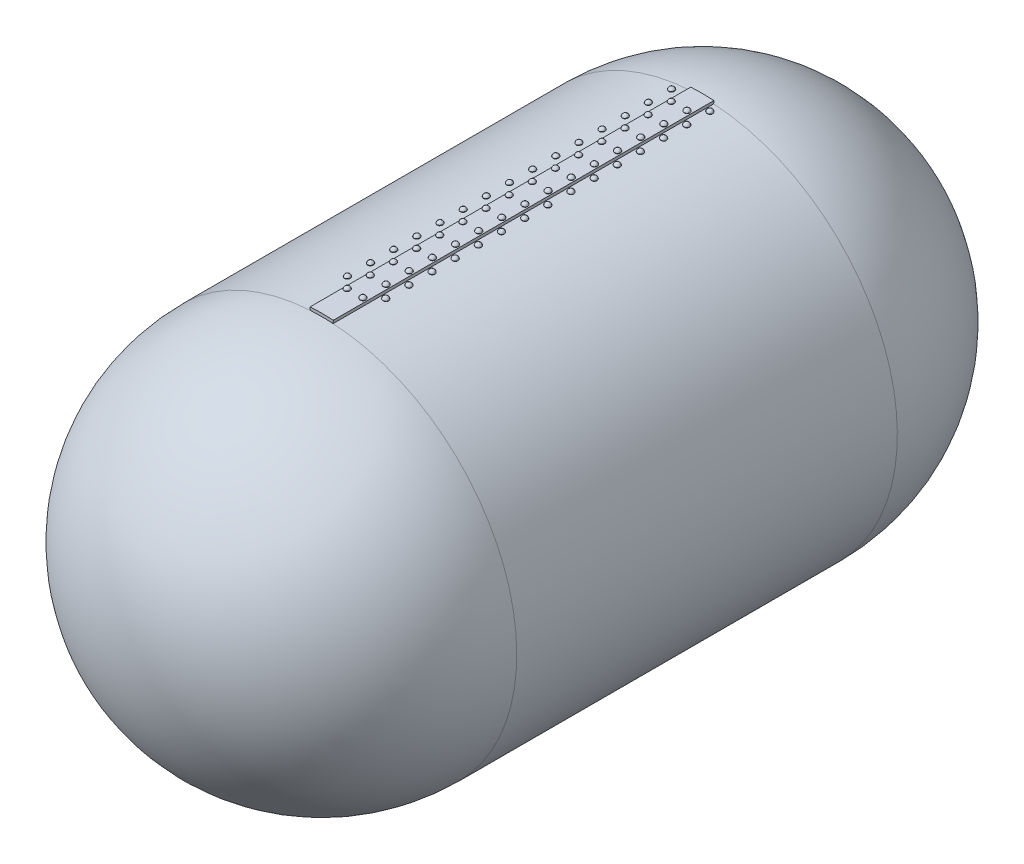
SolidWorks part; units mm, degrees
ref_plane "Front Plane" through (0, 0, 0) normal (0, 0, 1) x (1, 0, 0)
ref_plane "Top Plane" through (0, 0, 0) normal (0, 1, 0) x (1, 0, 0)
ref_plane "Right Plane" through (0, 0, 0) normal (1, 0, 0) x (0, 0, -1)
sketch "Sketch1" plane through (0, 0, 0) normal (0, 0, 1) x (1, 0, 0)
  line L0 (0, 0) -> (0, 860.5105) construction
  line L1 (-73.1248, 1246.8576) -> (-72.0124, 1227.8901)
  line L2 (73.1248, 1246.8576) -> (72.0124, 1227.8901)
  circle A0 centre (0, 0) radius 1230
  circle A1 centre (0, 0) radius 1200
  arc A2 (73.1248, 1246.8576) -> (-73.1248, 1246.8576) centre (0, 0) ccw
  point P7 (0, 1249)
  dimension "D" = 2400
  dimension "t" = 30
  dimension "outer_strap_thick" = 19
  dimension "right_half_width_of_outer_strap" = 73.1667
  dimension "half_width_outer_strap" = 73.1667
extrude "Boss-Extrude1" add sketch "Sketch1" along normal blind 2400
sketch "Sketch2" plane through (0, 0, 0) normal (0, 0, 1) x (1, 0, 0)
  line L0 (0, 0) -> (-49.487, 1248.0192) construction
  line L1 (0, 0) -> (49.487, 1248.0192) construction
  line L2 (-49.487, 1248.0192) -> (-24.6093, 620.6252) construction
  line L3 (0, 0) -> (120.3132, 1243.1918) construction
  arc A0 (73.1248, 1246.8576) -> (-73.1248, 1246.8576) centre (0, 0) ccw construction
  point P0 (49.487, 1248.0192)
  point P1 (-49.487, 1248.0192)
  point P5 (0, 1249)
  point P13 (120.3132, 1243.1918)
  dimension "row1_rytdist_from_center" = 49.5
  dimension "row_2_rytdist_from_center" = 49.5
  dimension "outerinner pitch" = 71
ref_plane "Plane1" through (-49.487, 1248.0192, 0) normal (-0.0396, 0.9992, 0) x (0.9992, 0.0396, 0)
sketch "Sketch3" plane through (-49.487, 1248.0192, 0) normal (-0.0396, 0.9992, 0) x (0.9992, 0.0396, 0)
  line L0 (0, 0) -> (0, -2684.229) construction
ref_plane "Plane2" through (0, 0, 146) normal (0, 0, 1) x (1, 0, 0)
sketch "Sketch4" plane through (0, 0, 146) normal (0, 0, 1) x (1, 0, 0)
  line L0 (-49.487, 1248.0192) -> (-28.4471, 717.4102) construction
  line L1 (0, 0) -> (-49.487, 1248.0192) construction
  line L2 (-49.487, 1248.0192) -> (-65.9741, 1247.3655)
  line L3 (499.9202, 1269.8046) -> (-598.8943, 1226.2339) construction
  line L4 (-65.9741, 1247.3655) -> (-68.5172, 1251.3929)
  line L5 (-68.5172, 1251.3929) -> (-49.6505, 1252.141)
  line L6 (-49.6505, 1252.141) -> (-49.487, 1248.0192)
  dimension "rvt_rad" = 16.5
  dimension "taper_height" = 4.125
  dimension "taper_angle" = 120
revolve "Revolve1" add sketch "Sketch4" angle 360 about L0
sketch "Sketch6" plane through (0, 0, 146) normal (0, 0, 1) x (1, 0, 0)
  line L0 (-49.487, 1248.0192) -> (-24.6093, 620.6252) construction
  line L1 (-30.7837, 1252.8891) -> (-68.5172, 1251.3929) construction
  line L2 (-32.5567, 1249.5162) -> (-66.4827, 1248.171) construction
  line L3 (-68.5172, 1251.3929) -> (-65.9741, 1247.3655) construction
  line L4 (-33, 1248.673) -> (-30.7837, 1252.8891) construction
  line L6 (-49.6505, 1252.141) -> (-50.2792, 1267.9963)
  line L7 (-49.6505, 1252.141) -> (-68.5172, 1251.3929)
  line L8 (-49.5197, 1248.8436) -> (-24.271, 612.0924) construction
  arc A0 (-68.5172, 1251.3929) -> (-50.2792, 1267.9963) centre (-49.5197, 1248.8436) cw
  point P0 (-49.5197, 1248.8436)
  point P11 (-49.5197, 1248.8436)
  point P15 (-49.5197, 1248.8436)
  dimension "arc_center_dist" = 3.3
revolve "Revolve2" add sketch "Sketch6" angle 360 about L6
mirror "Mirror1" about plane through (0, 0, 0) normal (1, 0, 0) of bodies 103
pattern_linear "LPattern1" count 15 spacing 146 along (0, 0, 1) of bodies 103
pattern_linear "LPattern2" count 15 spacing 146 along (0, 0, 1) of bodies 104
sketch "Sketch7" plane through (0, 0, 0) normal (1, 0, 0) x (0, 0, -1)
  line L0 (0, 0) -> (0, -1230)
  line L2 (0, 0) -> (1230, 0)
  line L3 (0, -1230) -> (0, 1227.8901) construction
  arc A0 (0, -1230) -> (1230, 0) centre (0, 0) ccw
revolve "Revolve3" add sketch "Sketch7" angle 360 about L2
ref_plane "Plane3" through (0, 0, 1200) normal (0, 0, 1) x (1, 0, 0)
mirror "Mirror2" about plane through (0, 0, 1200) normal (0, 0, 1) of "Revolve3"
ref_plane "Plane4" through (120.3132, 1243.1918, 0) normal (0.0963, 0.9953, 0) x (0.9953, -0.0963, 0)
sketch "Sketch8" plane through (120.3132, 1243.1918, 0) normal (0.0963, 0.9953, 0) x (0.9953, -0.0963, 0)
  line L0 (0, 0) -> (0, -3024.3198) construction
ref_plane "Plane5" through (0, 0, 73) normal (0, 0, 1) x (1, 0, 0)
sketch "Sketch9" plane through (0, 0, 73) normal (0, 0, 1) x (1, 0, 0)
  line L0 (120.3132, 1243.1918) -> (103.8899, 1244.7812)
  line L1 (696.3648, 1187.4428) -> (-455.7384, 1298.9407) construction
  line L2 (103.8899, 1244.7812) -> (101.9167, 1249.1164)
  line L3 (120.3132, 1243.1918) -> (120.7105, 1247.2976)
  line L4 (120.7105, 1247.2976) -> (101.9167, 1249.1164)
  dimension "rvt_dia" = 16.5
  dimension "taper_angle" = 120
  dimension "taper_height" = 4.125
revolve "Revolve4" add sketch "Sketch9" angle 360 about L3
sketch "Sketch11" plane through (0, 0, 73) normal (0, 0, 1) x (1, 0, 0)
  line L0 (137.29, 1242.3776) -> (103.4953, 1245.6482) construction
  line L1 (101.9167, 1249.1164) -> (103.8899, 1244.7812) construction
  line L2 (696.3648, 1187.4428) -> (-455.7384, 1298.9407) construction
  line L3 (139.5043, 1245.4788) -> (101.9167, 1249.1164) construction
  line L4 (136.7364, 1241.6024) -> (139.5043, 1245.4788) construction
  line L5 (0, 0) -> (120.3132, 1243.1918) construction
  line L6 (120.7105, 1247.2976) -> (122.239, 1263.0916)
  line L7 (120.7105, 1247.2976) -> (101.9167, 1249.1164)
  arc A0 (101.9167, 1249.1164) -> (122.239, 1263.0916) centre (120.3926, 1244.0129) cw
  point P0 (120.3926, 1244.0129)
  point P6 (120.3926, 1244.0129)
  dimension "center_arc_dist" = 3.3
revolve "Revolve5" add sketch "Sketch11" angle 360 about L6
mirror "Mirror3" about plane through (0, 0, 0) normal (1, 0, 0) of bodies 122
pattern_linear "LPattern3" count 15 spacing 146 along (0, 0, 1) of bodies 122
pattern_linear "LPattern4" count 15 spacing 146 along (0, 0, 1) of bodies 123
